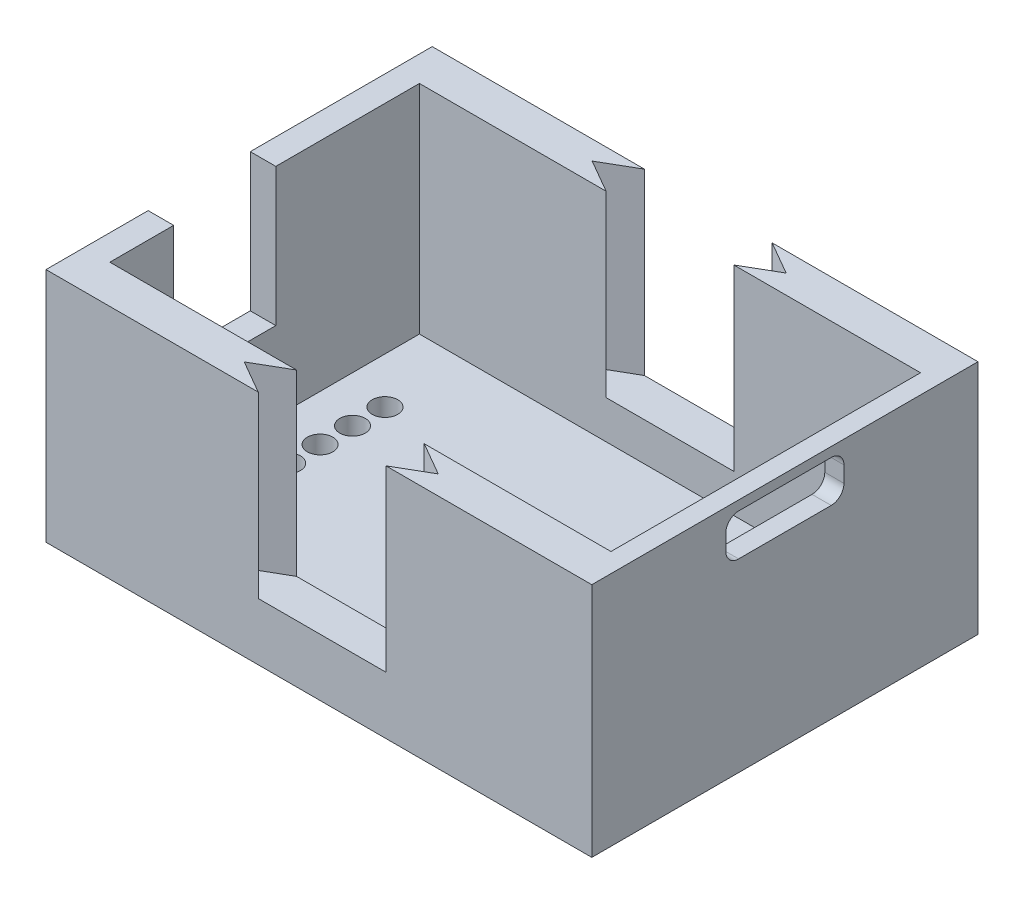
SolidWorks part; units mm, degrees
ref_plane "Front Plane" through (0, 0, 0) normal (0, 0, 1) x (1, 0, 0)
ref_plane "Top Plane" through (0, 0, 0) normal (0, 1, 0) x (1, 0, 0)
ref_plane "Right Plane" through (0, 0, 0) normal (1, 0, 0) x (0, 0, -1)
sketch "Sketch1" plane through (0, 0, 0) normal (0, 1, 0) x (1, 0, 0)
  line L1 (-19.625, -12.125) -> (19.625, -12.125)
  line L2 (-19.625, -12.125) -> (-19.625, 12.125)
  line L3 (-19.625, 12.125) -> (19.625, 12.125)
  line L4 (19.625, -12.125) -> (19.625, 12.125)
  line L5 (-19.625, -12.125) -> (19.625, 12.125) construction
  line L6 (-19.625, 12.125) -> (19.625, -12.125) construction
  point P0 (0, 0)
  dimension "D1" = 39.25
  dimension "D2" = 24.25
extrude "Boss-Extrude1" add sketch "Sketch1" along normal blind 1.5
sketch "Sketch2" plane through (0, 0, 0) normal (0, 1, 0) x (1, 0, 0)
  line L6 (21.125, 15.125) -> (-21.625, 15.125)
  line L9 (21.125, 15.125) -> (21.125, -15.125)
  line L10 (21.125, -15.125) -> (-21.625, -15.125)
  line L11 (-21.625, 15.125) -> (-21.625, -15.125)
  line L13 (19.625, -12.125) -> (19.625, 12.125)
  line L14 (19.625, 12.125) -> (-19.625, 12.125)
  line L15 (-19.625, 12.125) -> (-19.625, -12.125)
  line L16 (-19.625, -12.125) -> (19.625, -12.125)
  line L17 (19.625, -12.125) -> (19.625, 12.125)
  line L18 (19.625, 12.125) -> (-19.625, 12.125)
  line L19 (-19.625, 12.125) -> (-19.625, -12.125)
  line L20 (-19.625, -12.125) -> (19.625, -12.125)
  point P0 (0, 0)
  dimension "D1" = 3
  dimension "D2" = 3
  dimension "D3" = 0
  dimension "D4" = 2
  dimension "D5" = 1.5
extrude "Boss-Extrude2" add sketch "Sketch2" along normal offset from surface (18.5 mm away) 17 up to face at (0, 1.5, 0) offset beyond the face yes
sketch "Sketch3" plane through (0, 18.5, 0) normal (0, 1, 0) x (1, 0, 0)
  line L1 (-19.625, 0.875) -> (-21.625, 0.875)
  line L2 (-19.625, 0.875) -> (-19.625, -7.125)
  line L3 (-19.625, -7.125) -> (-21.625, -7.125)
  line L4 (-21.625, 0.875) -> (-21.625, -7.125)
  line L7 (-19.625, -12.125) -> (19.625, -12.125) construction
  line L8 (-21.625, -15.125) -> (-21.625, 15.125) construction
  line L9 (-19.625, -12.125) -> (-19.625, 12.125) construction
  dimension "D1" = 8
  dimension "D2" = 5
extrude "Cut-Extrude1" cut sketch "Sketch3" against normal offset from surface (10.8 mm away) 6.2 up to face at (0, 1.5, 0)
sketch "Sketch4" plane through (21.125, 0, 0) normal (1, 0, 0) x (0, 0, -1)
  line L1 (-3.625, 14.5) -> (3.625, 14.5)
  line L2 (-4.625, 15.5) -> (-4.625, 16.75)
  line L3 (-3.625, 17.75) -> (3.625, 17.75)
  line L4 (4.625, 15.5) -> (4.625, 16.75)
  line L5 (-4.625, 14.5) -> (4.625, 17.75) construction
  line L6 (-4.625, 17.75) -> (4.625, 14.5) construction
  line L7 (-12.125, 1.5) -> (12.125, 1.5) construction
  arc A0 (-3.625, 14.5) -> (-4.625, 15.5) centre (-3.625, 15.5) cw
  arc A1 (3.625, 14.5) -> (4.625, 15.5) centre (3.625, 15.5) ccw
  arc A2 (3.625, 17.75) -> (4.625, 16.75) centre (3.625, 16.75) cw
  arc A3 (-4.625, 16.75) -> (-3.625, 17.75) centre (-3.625, 16.75) cw
  point P0 (0, 16.125)
  dimension "D4" = 1
  dimension "D1" = 13
  dimension "D2" = 3.25
  dimension "D3" = 9.25
extrude "Cut-Extrude2" cut sketch "Sketch4" against normal up to next
sketch "Sketch6" plane through (0, 18.5, 0) normal (0, 1, 0) x (1, 0, 0)
  line L0 (0, 0) -> (0, 18.4461) construction
  line L1 (-5, 15.125) -> (-7.5981, 13.625)
  line L2 (-21.625, 15.125) -> (21.125, 15.125) construction
  line L3 (-7.5981, 13.625) -> (-5, 12.125)
  line L4 (19.625, 12.125) -> (-19.625, 12.125) construction
  line L5 (-5, 15.125) -> (-5, 12.125) construction
  line L6 (-5, 15.125) -> (5, 15.125)
  line L7 (-5, 12.125) -> (5, 12.125)
  line L8 (5, 15.125) -> (5, 12.125) construction
  line L9 (7.5981, 13.625) -> (5, 12.125)
  line L10 (5, 15.125) -> (7.5981, 13.625)
  line L11 (-7.5981, 0) -> (7.5981, 0) construction
  line L12 (-7.5981, -13.625) -> (-5, -12.125)
  line L13 (-5, -15.125) -> (-7.5981, -13.625)
  line L14 (-5, -15.125) -> (5, -15.125)
  line L15 (5, -15.125) -> (7.5981, -13.625)
  line L16 (7.5981, -13.625) -> (5, -12.125)
  line L17 (-5, -12.125) -> (5, -12.125)
  point P7 (-5, 13.625)
  point P16 (0, 12.125)
  point P18 (0, 15.125)
  point P20 (0, 0)
  dimension "D1" = 60
  dimension "D2" = 5
extrude "Cut-Extrude3" cut sketch "Sketch6" against normal offset from surface (14 mm away) 3 up to face at (0, 1.5, 0)
sketch "Sketch7" plane through (0, 1.5, 0) normal (0, 1, 0) x (1, 0, 0)
  line L0 (-16.025, -1.795) -> (-16.025, 0.745) construction
  line L2 (-19.625, 12.125) -> (-19.625, -12.125) construction
  line L3 (-17.525, -9.575) -> (15.575, -9.575) construction
  line L4 (-17.525, -9.575) -> (-17.525, 8.525) construction
  line L5 (-17.525, 8.525) -> (15.575, 8.525) construction
  line L6 (15.575, -9.575) -> (15.575, 8.525) construction
  line L7 (-19.625, 12.125) -> (-5, 12.125) construction
  circle A0 centre (-16.025, -6.875) radius 1
  circle A1 centre (-16.025, -4.335) radius 1
  circle A2 centre (-16.025, -1.795) radius 1
  circle A3 centre (-16.025, 0.745) radius 1
  circle A4 centre (-16.025, 3.285) radius 1
  circle A5 centre (-16.025, 5.825) radius 1
  point P18 (-16.025, -0.525)
  point P19 (-17.525, -0.525)
  point P20 (-15.825, -6.985)
  point P23 (-16.225, -7.4214)
  dimension "D2" = 2
  dimension "D3" = 2.1
  dimension "D6" = 0.5
  dimension "D4" = 18.1
  dimension "D5" = 33.1
  dimension "D7" = 3.6
  dimension "D8" = 2.54
  dimension "D1" = 6
extrude "Cut-Extrude4" cut sketch "Sketch7" against normal through all
